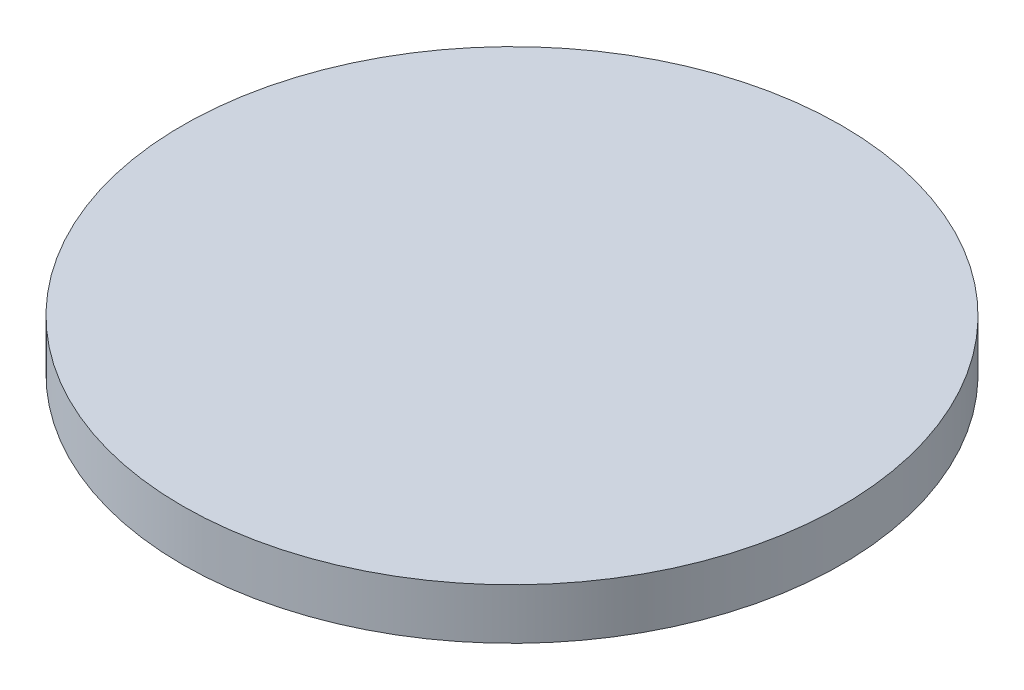
SolidWorks part; units mm, degrees
material "6061-T6 (SS)"
ref_plane "Front Plane" through (0, 0, 0) normal (0, 0, 1) x (1, 0, 0)
ref_plane "Top Plane" through (0, 0, 0) normal (0, 1, 0) x (1, 0, 0)
ref_plane "Right Plane" through (0, 0, 0) normal (1, 0, 0) x (0, 0, -1)
sketch "Sketch1" plane through (0, 0, 0) normal (0, 1, 0) x (1, 0, 0)
  circle A0 centre (0, 0) radius 82.5
  dimension "D1" = 165
extrude "Boss-Extrude1" add sketch "Sketch1" along normal blind 12.7
